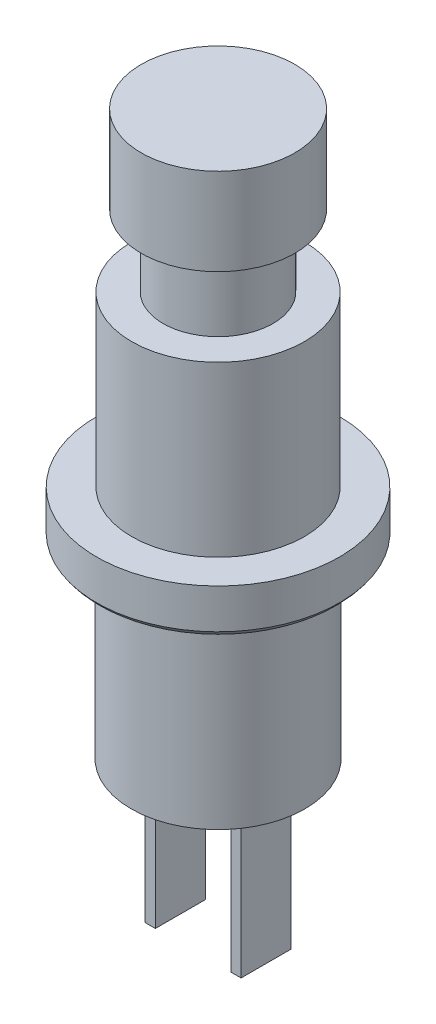
SolidWorks part; units mm, degrees
ref_plane "Front Plane" through (0, 0, 0) normal (0, 0, 1) x (1, 0, 0)
ref_plane "Top Plane" through (0, 0, 0) normal (0, 1, 0) x (1, 0, 0)
ref_plane "Right Plane" through (0, 0, 0) normal (1, 0, 0) x (0, 0, -1)
sketch "Sketch1" plane through (0, 0, 0) normal (0, 0, 1) x (1, 0, 0)
  line L0 (0, -223.6232) -> (0, 10961.7493) construction
  line L1 (0, 0) -> (3, 0)
  line L2 (3, 0) -> (3, -3.4)
  line L3 (3, -3.4) -> (2.15, -3.4)
  line L4 (2.15, -3.4) -> (2.15, -6.2)
  line L5 (2.15, -6.2) -> (3.375, -6.2)
  line L6 (3.375, -6.2) -> (3.375, -12.8)
  line L7 (3.375, -12.8) -> (4.75, -12.8)
  line L8 (4.75, -12.8) -> (4.75, -14.35)
  line L9 (3.9148, -14.8) -> (3.4, -14.8)
  line L10 (3.4, -14.8) -> (3.4, -22)
  line L11 (3.4, -22) -> (0, -22)
  line L12 (0, -22) -> (0, 0)
  arc A0 (4.75, -14.35) -> (3.9148, -14.8) centre (3.9148, -13.8) cw
  point P14 (3.45, -14.6792)
  point P18 (4.2023, -13.768)
  point P19 (3.7714, -12.0534)
  point P20 (4.1631, -14.8)
  dimension "D12" = 1
  dimension "D1" = 22
  dimension "D2" = 6.8
  dimension "D3" = 9.5
  dimension "D4" = 6
  dimension "D5" = 4.3
  dimension "D6" = 6.75
  dimension "D7" = 3.4
  dimension "D8" = 2.8
  dimension "D9" = 2
  dimension "D10" = 9.2
  dimension "D11" = 1.55
revolve "Revolve1" add sketch "Sketch1" angle 360 about L0
sketch "Sketch2" plane through (0, -22, 0) normal (0, -1, 0) x (1, 0, 0)
  line L0 (-1.475, 0) -> (1.475, 0) construction
  line L1 (-1.875, 0.975) -> (-1.475, 0.975)
  line L2 (-1.875, 0.975) -> (-1.875, -0.975)
  line L3 (-1.875, -0.975) -> (-1.475, -0.975)
  line L4 (-1.475, 0.975) -> (-1.475, -0.975)
  line L5 (1.475, 0.975) -> (1.875, 0.975)
  line L6 (1.475, 0.975) -> (1.475, -0.975)
  line L7 (1.475, -0.975) -> (1.875, -0.975)
  line L8 (1.875, 0.975) -> (1.875, -0.975)
  point P10 (0, 0)
  dimension "D1" = 0.4
  dimension "D2" = 1.95
  dimension "D3" = 2.95
extrude "Boss-Extrude1" add sketch "Sketch2" along normal blind 6
